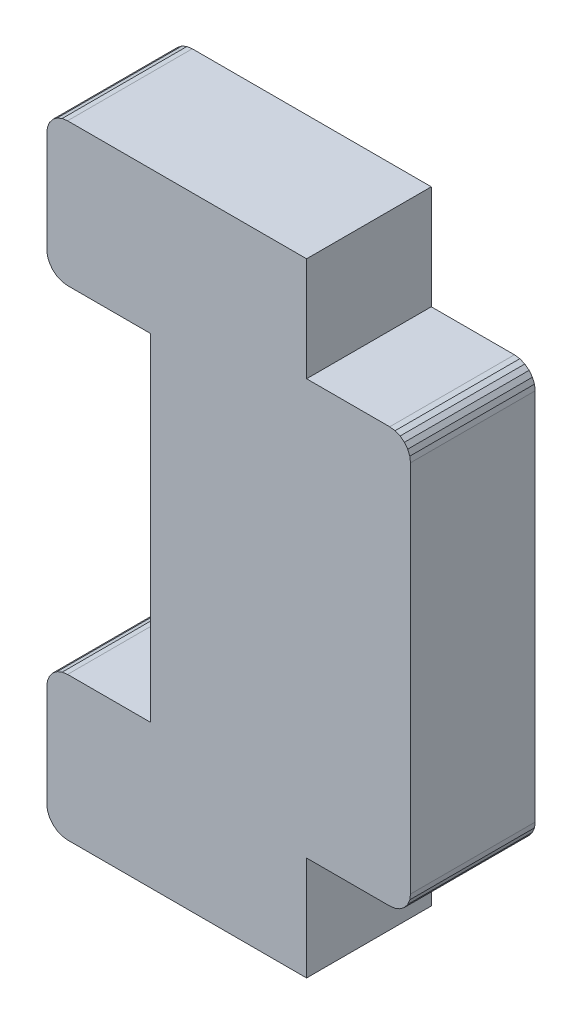
SolidWorks part; units mm, degrees
ref_plane "Plano frontal" through (0, 0, 0) normal (0, 0, 1) x (1, 0, 0)
ref_plane "Plano superior" through (0, 0, 0) normal (0, 1, 0) x (1, 0, 0)
ref_plane "Plano direito" through (0, 0, 0) normal (1, 0, 0) x (0, 0, -1)
sketch "Model" plane through (0, 0, 0) normal (0, 0, 1) x (1, 0, 0)
  line L0 (28.3852, 9.048) -> (28.3511, 9.3068)
  line L1 (28.4851, 14.7068) -> (28.3852, 14.4656)
  line L2 (28.644, 14.9139) -> (28.4851, 14.7068)
  line L3 (28.8511, 15.0728) -> (28.644, 14.9139)
  line L4 (29.3511, 31.4068) -> (33.3511, 31.4068)
  line L5 (29.3511, 8.3068) -> (40.8511, 8.3068)
  line L6 (29.3511, 15.2068) -> (29.0923, 15.1727)
  line L7 (29.0923, 8.3409) -> (28.8511, 8.4408)
  line L8 (28.8511, 8.4408) -> (28.644, 8.5997)
  line L9 (33.3511, 15.2068) -> (29.3511, 15.2068)
  line L10 (33.3511, 31.4068) -> (33.3511, 15.2068)
  line L11 (45.3511, 33.1413) -> (45.5582, 32.9824)
  line L12 (28.644, 8.5997) -> (28.4851, 8.8068)
  line L13 (45.7172, 13.8068) -> (45.8171, 14.048)
  line L14 (28.3852, 14.4656) -> (28.3511, 14.2068)
  line L15 (28.3511, 37.2753) -> (28.3852, 37.5341)
  line L16 (28.3852, 32.148) -> (28.3511, 32.4068)
  line L17 (45.8171, 32.5341) -> (45.8511, 32.2753)
  line L18 (45.8511, 32.2753) -> (45.8511, 14.3068)
  line L19 (28.4851, 8.8068) -> (28.3852, 9.048)
  line L20 (40.8511, 38.2753) -> (29.3511, 38.2753)
  line L21 (40.8511, 33.2753) -> (40.8511, 38.2753)
  line L22 (45.7172, 32.7753) -> (45.8171, 32.5341)
  line L23 (45.5582, 32.9824) -> (45.7172, 32.7753)
  line L24 (45.11, 33.2412) -> (45.3511, 33.1413)
  line L25 (44.8511, 33.2753) -> (45.11, 33.2412)
  line L26 (40.8511, 33.2753) -> (44.8511, 33.2753)
  line L27 (29.0923, 38.2412) -> (29.3511, 38.2753)
  line L28 (28.8511, 38.1413) -> (29.0923, 38.2412)
  line L29 (28.644, 37.9824) -> (28.8511, 38.1413)
  line L30 (28.4851, 37.7753) -> (28.644, 37.9824)
  line L31 (28.3852, 37.5341) -> (28.4851, 37.7753)
  line L32 (28.3511, 37.2753) -> (28.3511, 32.4068)
  line L33 (28.4851, 31.9068) -> (28.3852, 32.148)
  line L34 (28.644, 31.6997) -> (28.4851, 31.9068)
  line L35 (28.8511, 31.5408) -> (28.644, 31.6997)
  line L36 (29.0923, 31.4409) -> (28.8511, 31.5408)
  line L37 (29.3511, 31.4068) -> (29.0923, 31.4409)
  line L38 (29.0923, 15.1727) -> (28.8511, 15.0728)
  line L39 (28.3511, 14.2068) -> (28.3511, 9.3068)
  line L40 (29.3511, 8.3068) -> (29.0923, 8.3409)
  line L41 (40.8511, 13.3068) -> (40.8511, 8.3068)
  line L42 (44.8511, 13.3068) -> (40.8511, 13.3068)
  line L43 (44.8511, 13.3068) -> (45.11, 13.3409)
  line L44 (45.11, 13.3409) -> (45.3511, 13.4408)
  line L45 (45.3511, 13.4408) -> (45.5582, 13.5997)
  line L46 (45.5582, 13.5997) -> (45.7172, 13.8068)
  line L47 (45.8171, 14.048) -> (45.8511, 14.3068)
extrude "Ressalto-extrusão1" add sketch "Model" along normal blind 6
ref_plane "Plano1" through (0, 0, 3) normal (0, 0, 1) x (1, 0, 0)
ref_plane "Plano2" through (0, 23.291, 0) normal (0, 1, 0) x (1, 0, 0)
